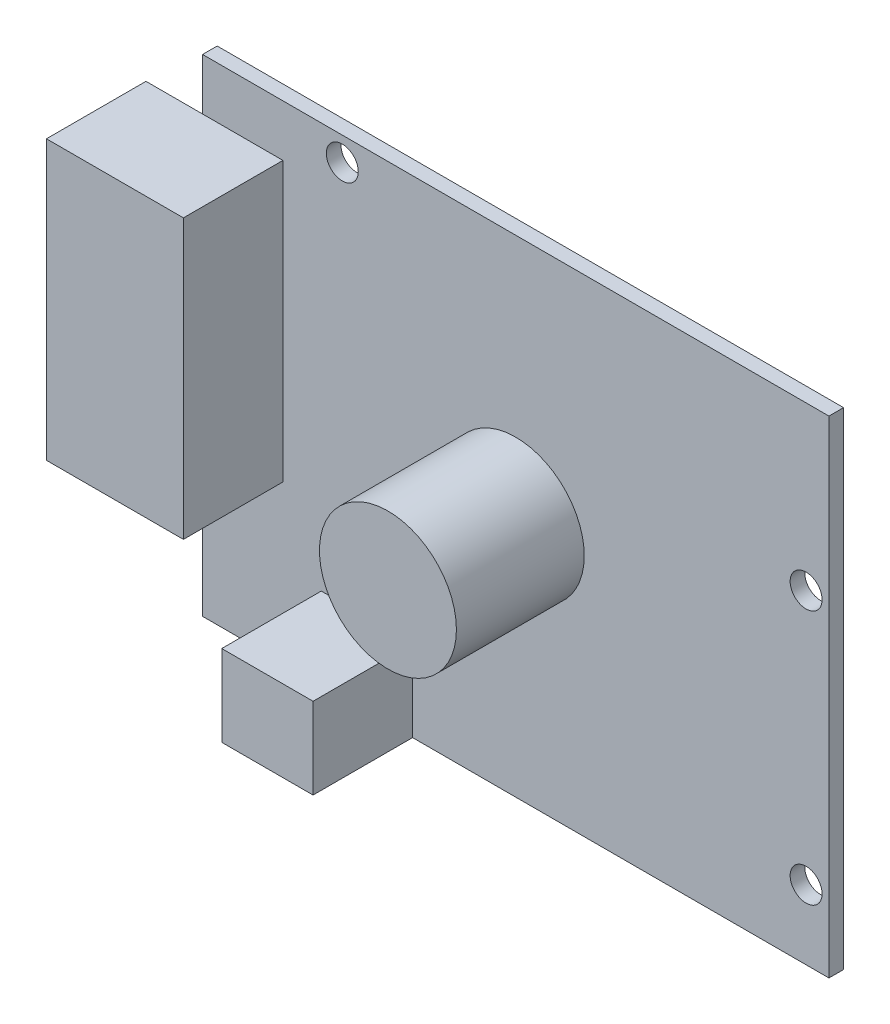
SolidWorks part; units mm, degrees
ref_plane "Front Plane" through (0, 0, 0) normal (0, 0, 1) x (1, 0, 0)
ref_plane "Top Plane" through (0, 0, 0) normal (0, 1, 0) x (1, 0, 0)
ref_plane "Right Plane" through (0, 0, 0) normal (1, 0, 0) x (0, 0, -1)
sketch "Sketch1" plane through (0, 0, 0) normal (0, 0, 1) x (1, 0, 0)
  line L1 (-34.3, 26.65) -> (34.3, 26.65)
  line L2 (-34.3, 26.65) -> (-34.3, -26.65)
  line L3 (-34.3, -26.65) -> (34.3, -26.65)
  line L4 (34.3, 26.65) -> (34.3, -26.65)
  point P4 (0, 26.65)
  point P6 (-34.3, 0)
  dimension "D1" = 68.6
  dimension "D2" = 53.3
extrude "Boss-Extrude1" add sketch "Sketch1" along normal blind 1.6
sketch "Sketch2" plane through (0, 0, 1.6) normal (0, 0, 1) x (1, 0, 0)
  line L0 (-34.3, 26.65) -> (-34.3, -26.65) construction
  line L1 (-40.5, 21) -> (-25.5, 21)
  line L2 (-40.5, 21) -> (-40.5, -9.5)
  line L3 (-40.5, -9.5) -> (-25.5, -9.5)
  line L4 (-25.5, 21) -> (-25.5, -9.5)
  line L5 (-21.3, -17.75) -> (-11.3, -17.75)
  line L6 (-21.3, -17.75) -> (-21.3, -26.65)
  line L7 (-21.3, -26.65) -> (-11.3, -26.65)
  line L8 (-11.3, -17.75) -> (-11.3, -26.65)
  line L9 (34.3, 26.65) -> (-34.3, 26.65) construction
  line L11 (-34.3, -26.65) -> (34.3, -26.65) construction
  dimension "D1" = 13
  dimension "D2" = 6.2
  dimension "D3" = 5.65
  dimension "D4" = 30.5
  dimension "D5" = 8.9
  dimension "D7" = 10
  dimension "D8" = 15
extrude "Boss-Extrude2" add sketch "Sketch2" along normal blind 10.9
sketch "Sketch3" plane through (0, 0, 1.6) normal (0, 0, 1) x (1, 0, 0)
  line L0 (-34.3, -26.65) -> (-21.3, -26.65) construction
  line L1 (-34.3, 26.65) -> (-34.3, 21) construction
  circle A0 centre (-19, 24.05) radius 1.75
  circle A1 centre (-20.3, -24.15) radius 1.75
  circle A2 centre (31.8, -19.05) radius 1.75
  circle A3 centre (31.8, 8.85) radius 1.75
  dimension "D7" = 3.5
  dimension "D1" = 27.9
  dimension "D2" = 50.8
  dimension "D3" = 1.3
  dimension "D4" = 15.2
  dimension "D5" = 2.5
  dimension "D6" = 5.1
  dimension "D8" = 14
extrude "Cut-Extrude1" cut sketch "Sketch3" against normal through all
sketch "Sketch4" plane through (0, 0, 1.6) normal (0, 0, 1) x (1, 0, 0)
  circle A0 centre (0, 0) radius 7.5
  dimension "D1" = 15
extrude "Boss-Extrude3" add sketch "Sketch4" along normal blind 14
